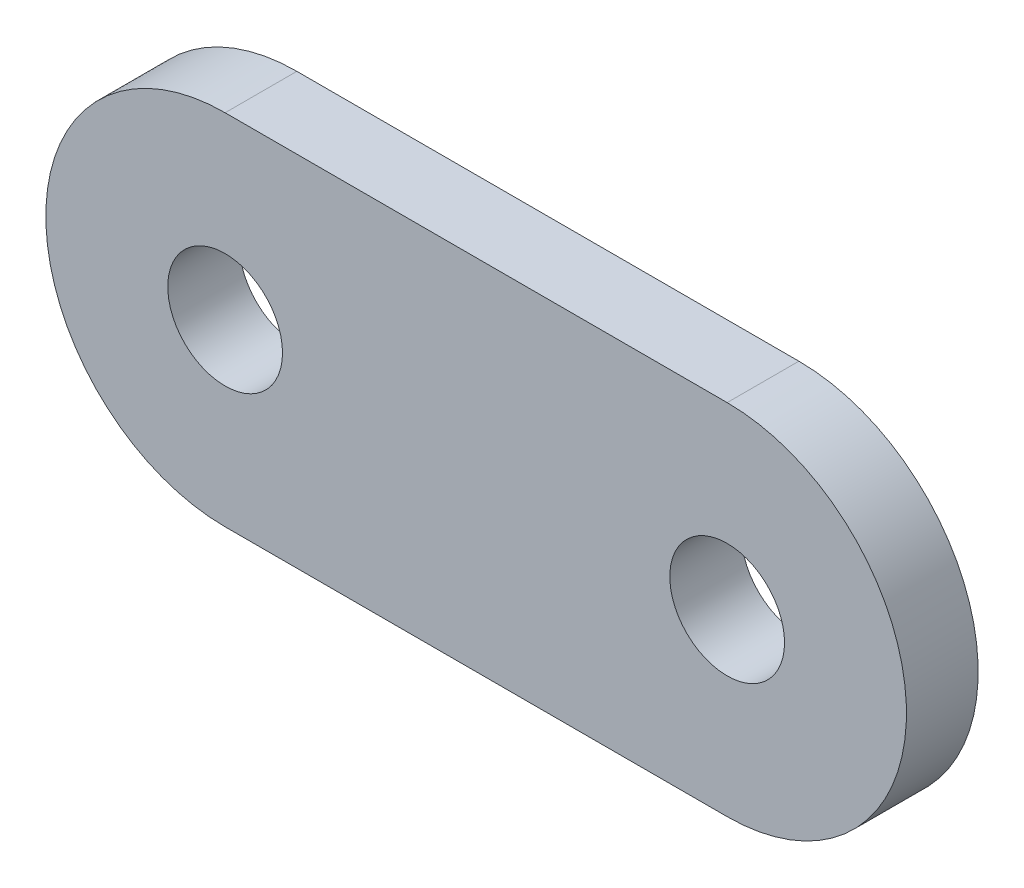
SolidWorks part; units mm, degrees
ref_plane "Plano frontal" through (0, 0, 0) normal (0, 0, 1) x (1, 0, 0)
ref_plane "Plano superior" through (0, 0, 0) normal (0, 1, 0) x (1, 0, 0)
ref_plane "Plano direito" through (0, 0, 0) normal (1, 0, 0) x (0, 0, -1)
sketch "Esboço1" plane through (0, 0, 0) normal (0, 0, 1) x (1, 0, 0)
  line L0 (-7, 0) -> (7, 0) construction
  line L1 (-7, 5) -> (7, 5)
  line L2 (-7, -5) -> (7, -5)
  arc A0 (-7, 5) -> (-7, -5) centre (-7, 0) ccw
  arc A1 (7, -5) -> (7, 5) centre (7, 0) ccw
  circle A2 centre (7, 0) radius 1.6
  circle A3 centre (-7, 0) radius 1.6
  point P2 (0, 0)
  dimension "D1" = 3.2
  dimension "D2" = 10
  dimension "D3" = 14
extrude "Ressalto-extrusão1" add sketch "Esboço1" along normal blind 2
